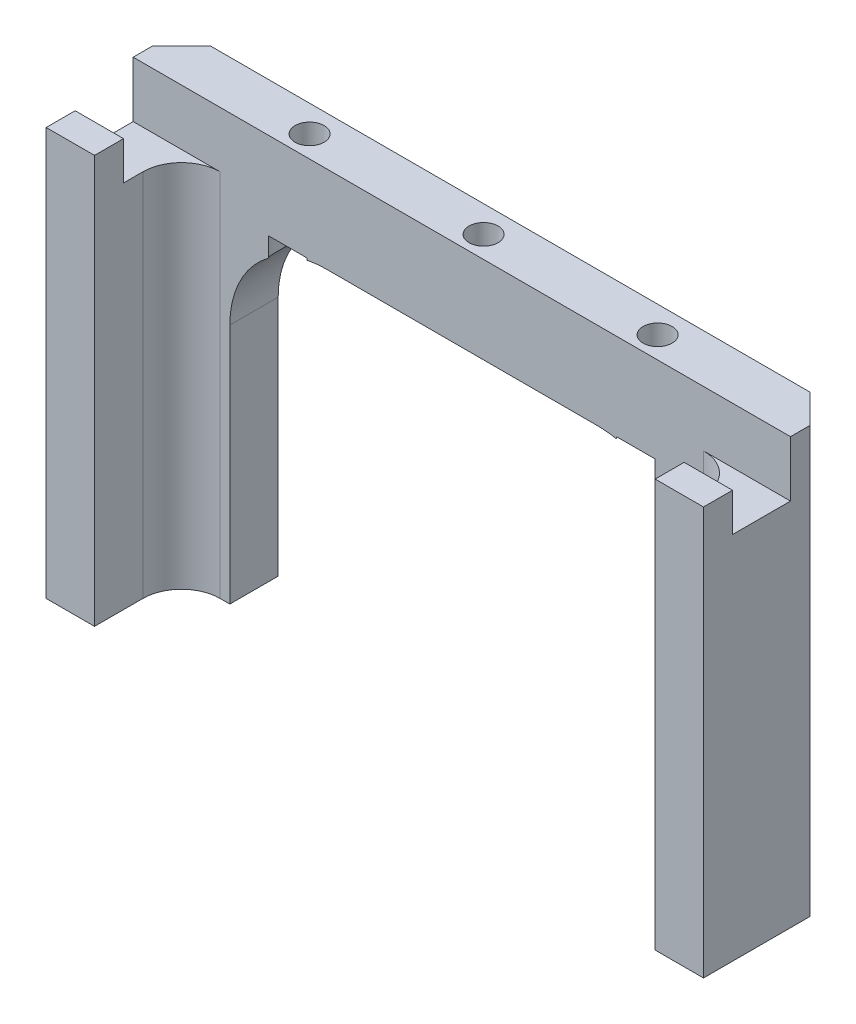
SolidWorks part; units mm, degrees
ref_plane "Front Plane" through (0, 0, 0) normal (0, 0, 1) x (1, 0, 0)
ref_plane "Top Plane" through (0, 0, 0) normal (0, 1, 0) x (1, 0, 0)
ref_plane "Right Plane" through (0, 0, 0) normal (1, 0, 0) x (0, 0, -1)
sketch "Sketch1" plane through (0, 0, 0) normal (0, 1, 0) x (1, 0, 0)
  line L0 (34, 0) -> (-34, 0)
  line L1 (-34, 0) -> (-34, -14)
  line L2 (-34, -14) -> (-29, -14)
  line L3 (-29, -14) -> (-29, -5)
  line L4 (-29, -5) -> (29, -5)
  line L5 (0, 15.0985) -> (0, -21.7899) construction
  line L6 (29, -14) -> (29, -5)
  line L7 (34, -14) -> (29, -14)
  line L8 (34, 0) -> (34, -14)
  point P11 (0, -5)
  point P14 (0, 0)
  dimension "D1" = 5
  dimension "D2" = 5
  dimension "D3" = 9
  dimension "D4" = 68
extrude "Boss-Extrude1" add sketch "Sketch1" against normal blind 44
sketch "Sketch2" plane through (0, 0, 0) normal (0, 0, -1) x (-1, 0, 0)
  line L0 (29, -44) -> (-29, -44) construction
  line L1 (24, -44) -> (-24, -44)
  line L2 (24, -44) -> (24, -9)
  line L3 (24, -9) -> (-24, -9)
  line L4 (-24, -44) -> (-24, -9)
  point P6 (0, -9)
  dimension "D1" = 48
  dimension "D2" = 35
extrude "Cut-Extrude1" cut sketch "Sketch2" against normal through all
fillet "Fillet1" radius 10 2 edges at (24, -9, 2.5) (-24, -9, 2.5)
sketch "Sketch3" plane through (0, -9, 0) normal (0, -1, 0) x (1, 0, 0)
  line L0 (-18, 2.75) -> (18, 2.75) construction
  line L1 (-14, 0) -> (14, 0) construction
  circle A0 centre (0, 2.75) radius 1.5
  circle A1 centre (-18, 2.75) radius 1.5
  circle A2 centre (18, 2.75) radius 1.5
  point P2 (0, 2.75)
  dimension "D1" = 3
  dimension "D2" = 2.75
  dimension "D3" = 18
extrude "Cut-Extrude2" cut sketch "Sketch3" against normal through all both and the other way through all
chamfer "Chamfer1" distance 3 angle 45 2 edges at (-34, -22, 0) (34, -22, 0)
sketch "Sketch4" plane through (0, 0, 0) normal (1, 0, 0) x (0, 0, -1)
  line L0 (-5, -44) -> (-5, 0) construction
  line L1 (-14, 0) -> (-5, 0)
  line L2 (-14, 0) -> (-14, -1.8)
  line L3 (-14, -1.8) -> (-5, -1.8)
  line L4 (-5, 0) -> (-5, -1.8)
  dimension "D2" = 1.8
extrude "Cut-Extrude3" cut sketch "Sketch4" against normal through all both and the other way through all
sketch "Sketch5" plane through (0, 0, 0) normal (1, 0, 0) x (0, 0, -1)
  line L1 (-5, -1.8) -> (-11, -1.8)
  line L2 (-5, -1.8) -> (-5, -5.7714)
  line L3 (-5, -5.7714) -> (-11, -5.7714)
  line L4 (-11, -1.8) -> (-11, -5.7714)
  dimension "D1" = 6
extrude "Cut-Extrude4" cut sketch "Sketch5" against normal through all both and the other way through all
sketch "Sketch6" plane through (0, -9, 0) normal (0, -1, 0) x (1, 0, 0)
  circle A0 centre (0, 2.75) radius 3
  circle A1 centre (18, 2.75) radius 3
  circle A2 centre (-18, 2.75) radius 3
  dimension "D1" = 6
extrude "Cut-Extrude6" cut sketch "Sketch6" along normal blind 11
fillet "Fillet2" radius 4 2 edges at (29, -24.8857, 5) (-29, -24.8857, 5)
